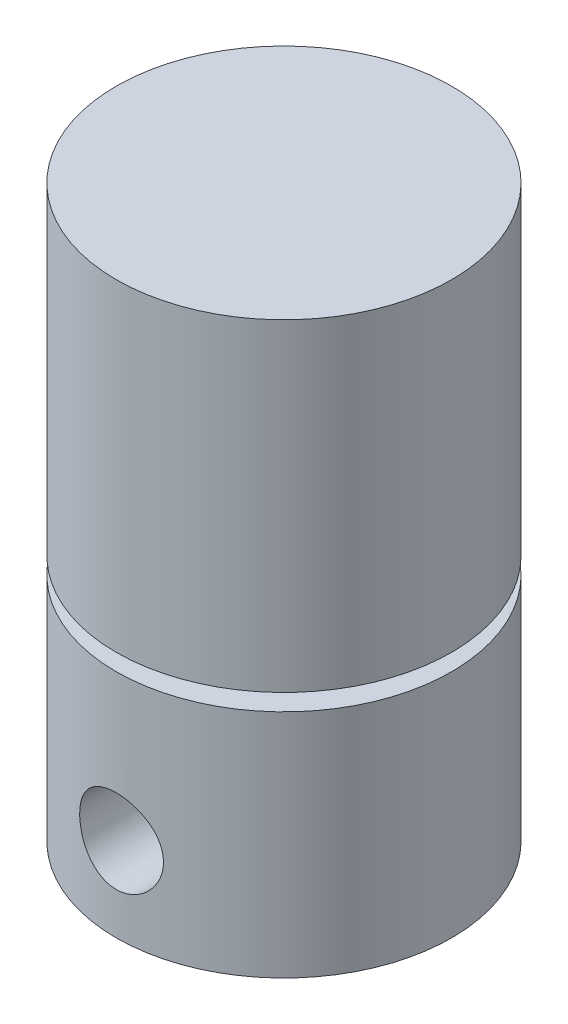
SolidWorks part; units mm, degrees
material "AISI 304"
ref_plane "Front Plane" through (0, 0, 0) normal (0, 0, 1) x (1, 0, 0)
ref_plane "Top Plane" through (0, 0, 0) normal (0, 1, 0) x (1, 0, 0)
ref_plane "Right Plane" through (0, 0, 0) normal (1, 0, 0) x (0, 0, -1)
sketch "Sketch1" plane through (0, 0, 0) normal (0, 1, 0) x (1, 0, 0)
  circle A0 centre (0, 0) radius 12.7
  dimension "D1" = 25.4
extrude "Boss-Extrude1" add sketch "Sketch1" along normal blind 17.4625
sketch "Sketch2" plane through (0, 17.4625, 0) normal (0, 1, 0) x (1, 0, 0)
  circle A0 centre (0, 0) radius 9.525
  dimension "D1" = 19.05
extrude "Boss-Extrude2" add sketch "Sketch2" along normal blind 1.27
sketch "Sketch3" plane through (0, 18.7325, 0) normal (0, 1, 0) x (1, 0, 0)
  circle A0 centre (0, 0) radius 12.7
  dimension "D1" = 25.4
extrude "Boss-Extrude3" add sketch "Sketch3" along normal blind 24.4475
sketch "Sketch4" plane through (0, 0, 0) normal (0, 0, 1) x (1, 0, 0)
  line L0 (0, 0) -> (0, 6.35) construction
  circle A0 centre (0, 6.35) radius 3.175
  dimension "D2" = 6.35
  dimension "D1" = 6.35
extrude "Cut-Extrude1" cut sketch "Sketch4" along normal up to next from offset 6.35
sketch "Sketch5" plane through (0, 0, 0) normal (0, 0, 1) x (1, 0, 0)
  line L0 (0, 0) -> (0, 6.35) construction
  circle A0 centre (0, 6.35) radius 3.175
  dimension "D2" = 6.35
  dimension "D1" = 6.35
extrude "Cut-Extrude2" cut sketch "Sketch5" against normal up to next from offset 9.398 offset against normal yes
sketch "Sketch6" plane through (0, 0, 0) normal (0, -1, 0) x (-1, 0, 0)
  line L0 (0, 0) -> (-9.525, 0) construction
  line L1 (0, -4.7802) -> (0, 4.7802) construction
  circle A0 centre (-9.525, 0) radius 1.5875
  circle A1 centre (9.525, 0) radius 1.5875
  point P6 (0, 0)
  dimension "D2" = 3.175
  dimension "D1" = 9.525
extrude "Cut-Extrude3" cut sketch "Sketch6" against normal blind 6.35
